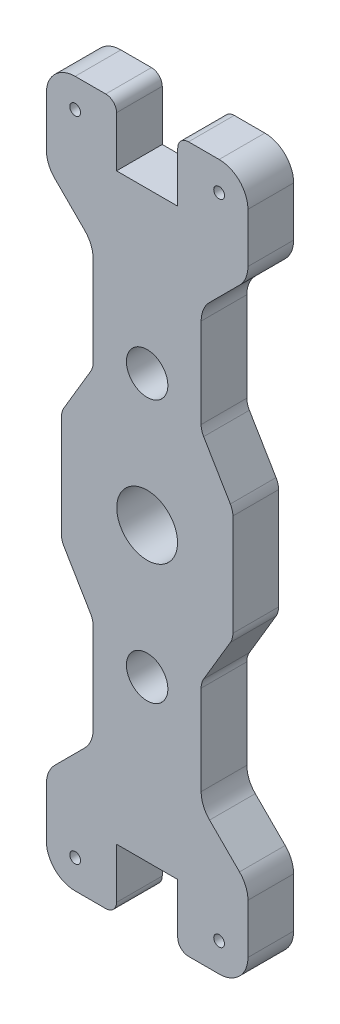
SolidWorks part; units mm, degrees
material "6061-T6 (SS)"
ref_plane "Front Plane" through (0, 0, 0) normal (0, 0, 1) x (1, 0, 0)
ref_plane "Top Plane" through (0, 0, 0) normal (0, 1, 0) x (1, 0, 0)
ref_plane "Right Plane" through (0, 0, 0) normal (1, 0, 0) x (0, 0, -1)
sketch "Sketch1" plane through (0, 0, 0) normal (0, 0, 1) x (1, 0, 0)
  line L1 (0, -6.985) -> (0, 6.985) construction
  line L2 (6.985, 0) -> (-6.985, 0) construction
  line L3 (-28, 72.9228) -> (-28, 90)
  line L4 (-20, 98) -> (-11.5, 98)
  line L5 (28, 90) -> (28, 72.9228)
  line L6 (28, 72.9228) -> (15, 59.9228)
  line L7 (15, 59.9228) -> (15, -59.9228)
  line L13 (-15, -59.9228) -> (-15, 59.9228)
  line L14 (-15, 59.9228) -> (-28, 72.9228)
  line L15 (0, -1000) -> (0, 49000) construction
  line L16 (-1000, 0) -> (49000, 0) construction
  line L17 (-8.5, 95) -> (-8.5, 81)
  line L18 (-8.5, 81) -> (8.5, 81)
  line L19 (8.5, 81) -> (8.5, 95)
  line L20 (11.5, 98) -> (20, 98)
  line L21 (-20, 98) -> (-20, 90) construction
  line L22 (-20, 90) -> (-28, 90) construction
  line L23 (-8.5, 81) -> (-22.2886, 67.2114) construction
  line L24 (-8.5, 81) -> (-28, 81) construction
  line L25 (28, -72.9228) -> (15, -59.9228)
  line L26 (28, -90) -> (28, -72.9228)
  line L27 (11.5, -98) -> (20, -98)
  line L28 (8.5, -81) -> (8.5, -95)
  line L29 (-8.5, -81) -> (8.5, -81)
  line L30 (-8.5, -95) -> (-8.5, -81)
  line L31 (-20, -98) -> (-11.5, -98)
  line L32 (-28, -72.9228) -> (-28, -90)
  line L33 (-15, -59.9228) -> (-28, -72.9228)
  circle A0 centre (0, 0) radius 8.4375
  circle A1 centre (-20, 90) radius 1.5
  circle A3 centre (20, 90) radius 1.5
  circle A4 centre (20, -90) radius 1.5
  circle A5 centre (-20, -90) radius 1.5
  arc A6 (-28, 90) -> (-20, 98) centre (-20, 90) cw
  arc A7 (20, 98) -> (28, 90) centre (20, 90) cw
  arc A8 (20, -98) -> (28, -90) centre (20, -90) ccw
  arc A9 (-28, -90) -> (-20, -98) centre (-20, -90) ccw
  arc A10 (-8.5, -95) -> (-11.5, -98) centre (-11.5, -95) cw
  arc A11 (11.5, -98) -> (8.5, -95) centre (11.5, -95) cw
  arc A12 (8.5, 95) -> (11.5, 98) centre (11.5, 95) cw
  arc A13 (-8.5, 95) -> (-11.5, 98) centre (-11.5, 95) ccw
  point P22 (0, 81)
  point P39 (15, 0)
  point P51 (-15, 0)
  point P53 (-8.5, -98)
  point P56 (8.5, -98)
  point P59 (8.5, 98)
  point P62 (-8.5, 98)
  dimension "D1" = 16.875
  dimension "D2" = 3
  dimension "D9" = 3
  dimension "D3" = 30
  dimension "D4" = 17
  dimension "D5" = 40
  dimension "D6" = 8
  dimension "D7" = 180
  dimension "D8" = 45
  dimension "D10" = 17
extrude "Boss-Extrude1" add sketch "Sketch1" along normal mid plane 12.7
fillet "Fillet1" radius 8 8 edges at (-28, 72.9228, 0) (-15, 59.9228, 0) (-28, -72.9228, 0) (-15, -59.9228, 0) (15, -59.9228, 0) (28, -72.9228, 0) (28, 72.9228, 0) (15, 59.9228, 0)
sketch "Sketch8" plane through (0, 0, 0) normal (0, 0, 1) x (1, 0, 0)
  line L0 (28, 76.2365) -> (28, 90) construction
  line L1 (28, 74.406) -> (-28, 74.406)
  line L2 (28, 74.406) -> (28, 98)
  line L3 (28, 98) -> (-28, 98)
  line L4 (-28, 74.406) -> (-28, 98)
  line L5 (-28, 90) -> (-28, 76.2365) construction
  line L6 (-11.5, 98) -> (-20, 98) construction
  line L7 (6.985, 0) -> (-6.985, 0) construction
  line L8 (28, -98) -> (-28, -98)
  line L9 (-28, -74.406) -> (-28, -98)
  line L10 (28, -74.406) -> (-28, -74.406)
  line L11 (28, -74.406) -> (28, -98)
  line L12 (28, -80) -> (-28, -80) construction
  line L13 (0, -80) -> (0, -74.406) construction
  line L14 (28, -90) -> (28, -76.2365) construction
  line L15 (28, 80) -> (-28, 80) construction
  line L16 (28, -74.406) -> (-28, 74.406) construction
  point P20 (0, -80)
  dimension "D1" = 160
  dimension "D2" = 159
extrude "Cut-Extrude1" [suppressed] cut sketch "Sketch8" against normal mid plane 3.35
sketch "Sketch4" plane through (0, 0, 6.35) normal (0, 0, 1) x (1, 0, 0)
  line L0 (0, 36.5125) -> (0, -36.5125) construction
  point P0 (0, 36.5125)
  point P2 (0, -36.5125)
  point P4 (0, 0)
  dimension "D2" = 73.025
hole_wizard "7/16 Clearance Hole4" positions "Sketch4" profile "Sketch5" hole size "7/16" standard "ANSI Inch" end condition through all
sketch "Sketch5" plane through (0, 36.5125, 6.35) normal (1, 0, 0) x (0, -1, 0)
  line L0 (0, 0) -> (0, 12.7)
  line L1 (0, 12.7) -> (5.7544, 12.7)
  line L2 (5.7544, 12.7) -> (5.7544, 0)
  line L5 (5.7544, 0) -> (0, 0)
  line L11 (0, -6.35) -> (0, 107.95) construction
  dimension "Thru Hole Dia." = 11.5087
  dimension "Thru Hole Depth" = 12.7
sketch "Sketch6" plane through (0, 0, 6.35) normal (0, 0, 1) x (1, 0, 0)
  line L0 (-15, 30.341) -> (-23.8125, 15.4813)
  line L1 (-15, 56.6091) -> (-15, -56.6091) construction
  line L2 (-23.8125, 15.4813) -> (-23.8125, -15.4813)
  line L3 (-23.8125, -15.4813) -> (-15, -30.341)
  line L4 (-15, -30.341) -> (-15, 30.341)
  line L5 (0, -6.985) -> (0, 6.985) construction
  line L6 (23.8125, -15.4813) -> (15, -30.341)
  line L7 (23.8125, 15.4813) -> (23.8125, -15.4813)
  line L8 (15, 30.341) -> (23.8125, 15.4813)
  line L9 (15, -30.341) -> (15, 30.341)
  point P4 (-15, 0)
  point P8 (-23.8125, 0)
  dimension "D1" = 30.9626
  dimension "D2" = 30.67
  dimension "D3" = 47.625
extrude "Boss-Extrude2" add sketch "Sketch6" against normal up to surface (12.7 mm away) up to face at (5.7544, 36.5125, -6.35)
fillet "Fillet2" radius 5 8 edges at (15, 30.341, 0) (23.8125, 15.4813, 0) (23.8125, -15.4813, 0) (15, -30.341, 0) (-15, -30.341, 0) (-23.8125, -15.4813, 0) (-23.8125, 15.4813, 0) (-15, 30.341, 0)
equation "\"D1@Fillet1\"=\"D6@Sketch1\""
equation "\"Shaft Size\"= 5in / 8"
equation "\"Bearing Screw Spacing\"= 2.875in"
equation "\"D1@Sketch1\"= \"Shaft Size\" + 1mm"
equation "\"D2@Sketch4\"= \"Bearing Screw Spacing\""
equation "\"Plate Thickness\"= 1in / 2"
equation "\"D1@Boss-Extrude1\"=\"Plate Thickness\""
